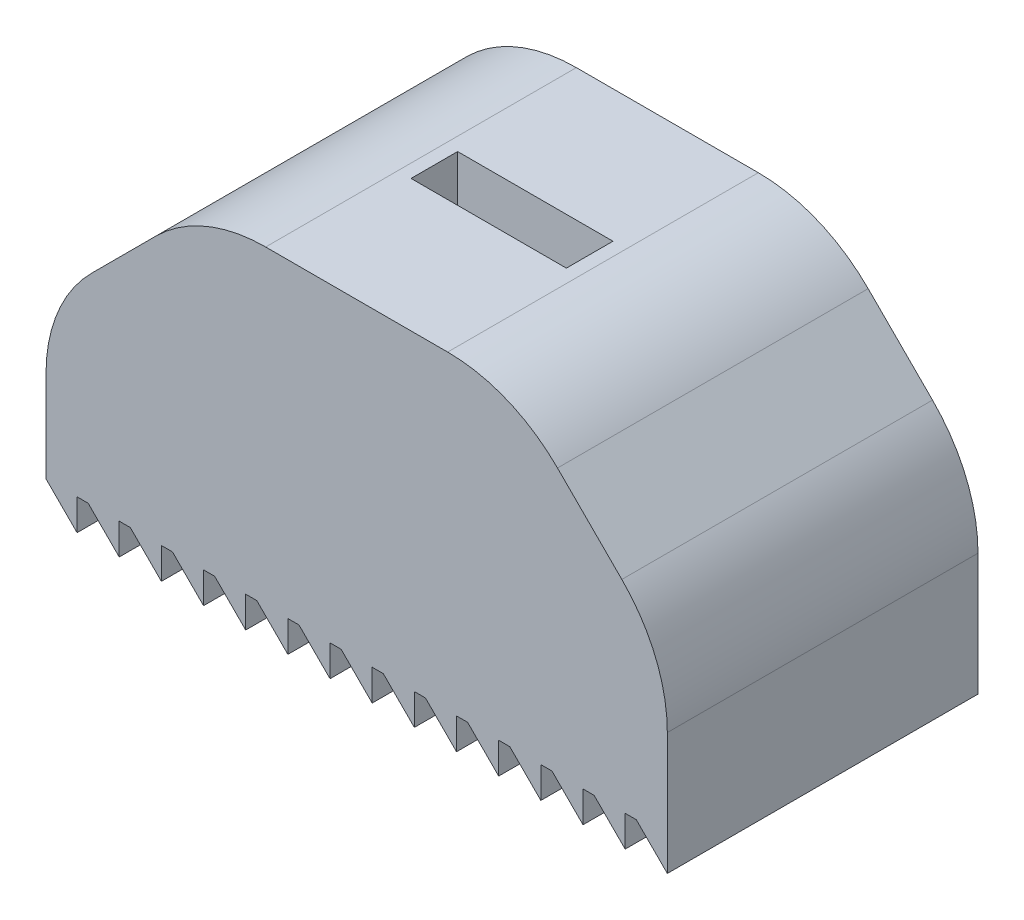
SolidWorks part; units mm, degrees
ref_plane "Спереди" through (0, 0, 0) normal (0, 0, 1) x (1, 0, 0)
ref_plane "Сверху" through (0, 0, 0) normal (0, 1, 0) x (1, 0, 0)
ref_plane "Справа" through (0, 0, 0) normal (1, 0, 0) x (0, 0, -1)
sketch "Sketch1" plane through (0, 0, 0) normal (0, 0, 1) x (1, 0, 0)
  line L0 (-10.271, 0) -> (9.729, 0)
  line L49 (-10.271, 0) -> (9.729, 0)
  line L50 (-20.271, -10) -> (-20.271, -20)
  line L51 (19.729, -10) -> (19.729, -20)
  line L52 (-18.271, -20) -> (-17.5568, -20)
  line L53 (-20.271, -20) -> (-18.271, -22)
  line L54 (-18.271, -22) -> (-18.271, -20)
  line L55 (-17.5568, -20) -> (-15.5568, -22)
  line L56 (-15.5568, -22) -> (-15.5568, -20)
  line L57 (-14.8425, -20) -> (-12.8425, -22)
  line L58 (-12.8425, -22) -> (-12.8425, -20)
  line L59 (-12.1282, -20) -> (-10.1282, -22)
  line L60 (-10.1282, -22) -> (-10.1282, -20)
  line L61 (-9.4139, -20) -> (-7.4139, -22)
  line L62 (-7.4139, -22) -> (-7.4139, -20)
  line L63 (-6.6996, -20) -> (-4.6996, -22)
  line L64 (-4.6996, -22) -> (-4.6996, -20)
  line L65 (-3.9853, -20) -> (-1.9853, -22)
  line L66 (-1.9853, -22) -> (-1.9853, -20)
  line L67 (-1.271, -20) -> (0.729, -22)
  line L68 (0.729, -22) -> (0.729, -20)
  line L69 (1.4432, -20) -> (3.4432, -22)
  line L70 (3.4432, -22) -> (3.4432, -20)
  line L71 (4.1575, -20) -> (6.1575, -22)
  line L72 (6.1575, -22) -> (6.1575, -20)
  line L73 (6.8718, -20) -> (8.8718, -22)
  line L74 (8.8718, -22) -> (8.8718, -20)
  line L75 (9.5861, -20) -> (11.5861, -22)
  line L76 (11.5861, -22) -> (11.5861, -20)
  line L77 (12.3004, -20) -> (14.3004, -22)
  line L78 (14.3004, -22) -> (14.3004, -20)
  line L79 (15.0147, -20) -> (17.0147, -22)
  line L80 (17.0147, -22) -> (17.0147, -20)
  line L81 (17.729, -20) -> (19.729, -22)
  line L82 (19.729, -22) -> (19.729, -20)
  line L83 (-20.271, -10) -> (-10.271, 0)
  line L84 (9.729, 0) -> (19.729, -10)
  line L85 (-15.5568, -20) -> (-14.8425, -20)
  line L86 (-12.8425, -20) -> (-12.1282, -20)
  line L87 (-10.1282, -20) -> (-9.4139, -20)
  line L88 (-7.4139, -20) -> (-6.6996, -20)
  line L89 (-4.6996, -20) -> (-3.9853, -20)
  line L90 (-1.9853, -20) -> (-1.271, -20)
  line L91 (0.729, -20) -> (1.4432, -20)
  line L92 (3.4432, -20) -> (4.1575, -20)
  line L93 (6.1575, -20) -> (6.8718, -20)
  line L94 (8.8718, -20) -> (9.5861, -20)
  line L95 (11.5861, -20) -> (12.3004, -20)
  line L96 (14.3004, -20) -> (15.0147, -20)
  line L97 (17.0147, -20) -> (17.729, -20)
  point P78 (0, 0)
  dimension "D3" = 2
  dimension "D4" = 45
  dimension "D6" = 0
  dimension "D5" = 15
extrude "Boss-Extrude1" add sketch "Sketch1" along normal blind 20 contours L80 L97 L81 L82 L51 L84 L0 L83 L50 L53 L54 L52 L55 L56 L85 L57 L58 L86 L59 L60 L87 L61 L62 L88 L63 L64 L89 L65 L66 L90 L67 L68 L91 L69 L70 L92 L71 L72 L93 L73 L74 L94 L75 L76 L95 L77 L78 L96 L79
sketch "Sketch2" plane through (0, 0, 0) normal (0, 1, 0) x (1, 0, 0)
  line L1 (-5.271, -11.5) -> (4.729, -11.5)
  line L2 (-5.271, -11.5) -> (-5.271, -8.5)
  line L3 (-5.271, -8.5) -> (4.729, -8.5)
  line L4 (4.729, -11.5) -> (4.729, -8.5)
  line L5 (-5.271, -11.5) -> (4.729, -8.5) construction
  line L6 (-5.271, -8.5) -> (4.729, -11.5) construction
  line L10 (-0.271, -10) -> (-10.271, -10) construction
  line L13 (-0.271, -10) -> (9.729, -10) construction
  line L16 (-5.271, -8.5) -> (-5.271, 0) construction
  line L17 (-10.271, 0) -> (9.729, 0) construction
  line L18 (-5.271, -11.5) -> (-5.271, -20) construction
  line L19 (-10.271, -20) -> (9.729, -20) construction
  point P0 (-0.271, -10)
  dimension "D2" = 3
  dimension "D3" = 10
extrude "Cut-Extrude1" cut sketch "Sketch2" against normal blind 10
fillet "Скругление1" radius 10 4 edges at (19.729, -10, 10) (9.729, 0, 10) (-20.271, -10, 10) (-10.271, 0, 10)
